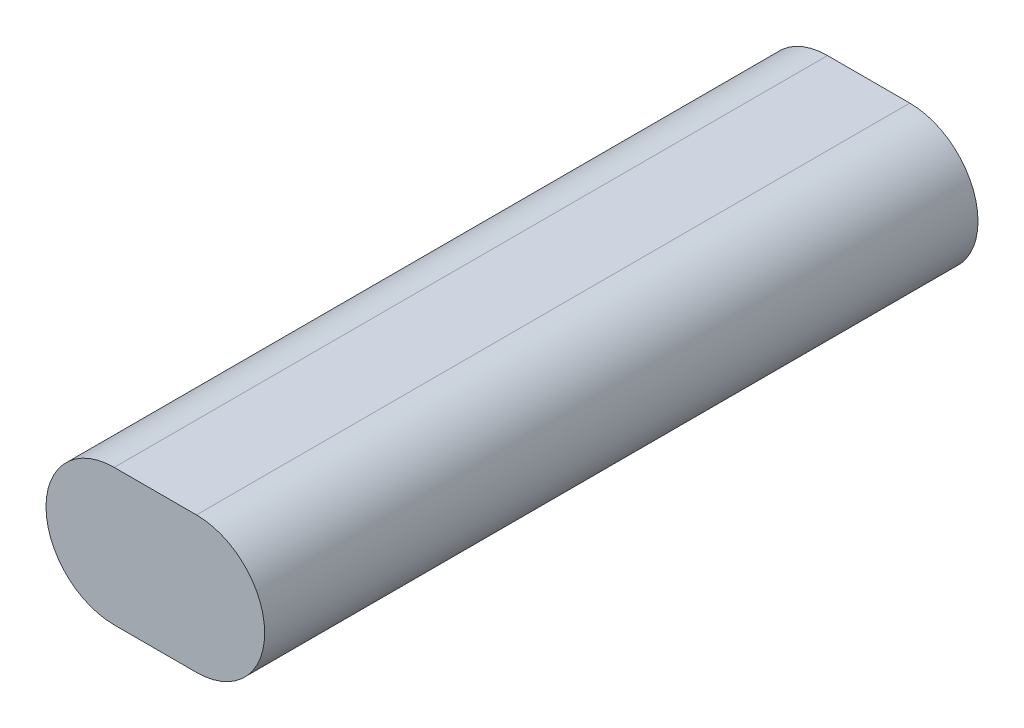
SolidWorks part; units mm, degrees
ref_plane "Front Plane" through (0, 0, 0) normal (0, 0, 1) x (1, 0, 0)
ref_plane "Top Plane" through (0, 0, 0) normal (0, 1, 0) x (1, 0, 0)
ref_plane "Right Plane" through (0, 0, 0) normal (1, 0, 0) x (0, 0, -1)
sketch "Sketch1" plane through (0, 0, 0) normal (0, 0, 1) x (1, 0, 0)
  line L0 (-12.573, 0) -> (12.573, 0) construction
  line L1 (-12.573, 11.557) -> (12.573, 11.557)
  line L2 (-12.573, -11.557) -> (12.573, -11.557)
  line L3 (-10.033, 0) -> (10.033, 0) construction
  line L4 (-10.033, 16.637) -> (10.033, 16.637)
  line L5 (-10.033, -16.637) -> (10.033, -16.637)
  line L6 (-24.13, 0) -> (-26.67, 0)
  line L7 (24.13, 0) -> (26.67, 0)
  arc A0 (-12.573, 11.557) -> (-12.573, -11.557) centre (-12.573, 0) ccw
  arc A1 (12.573, -11.557) -> (12.573, 11.557) centre (12.573, 0) ccw
  arc A2 (-10.033, 16.637) -> (-10.033, -16.637) centre (-10.033, 0) ccw
  arc A3 (10.033, -16.637) -> (10.033, 16.637) centre (10.033, 0) ccw
  point P2 (0, 0)
  point P8 (-24.13, 0)
  point P9 (24.13, 0)
  point P12 (0, 0)
  point P17 (-26.67, 0)
  dimension "D2" = 23.114
  dimension "D4" = 2.54
  dimension "D1" = 48.26
  dimension "D3" = 5.08
extrude "Boss-Extrude1" add sketch "Sketch1" against normal blind 168.91 contours L7 A3 L4 A2 L6 A0 L1 A1 | L5 A3 L7 A1 L2 A0 L6 A2
sketch "Sketch3" plane through (0, 0, 0) normal (0, 0, 1) x (1, 0, 0)
  line L0 (-10.033, 0) -> (10.033, 0) construction
  line L1 (-10.033, 16.637) -> (10.033, 16.637)
  line L2 (-10.033, -16.637) -> (10.033, -16.637)
  line L3 (-10.033, 16.637) -> (10.033, 16.637) construction
  arc A0 (-10.033, 16.637) -> (-10.033, -16.637) centre (-10.033, 0) ccw
  arc A1 (10.033, -16.637) -> (10.033, 16.637) centre (10.033, 0) ccw
  arc A2 (-10.033, 16.637) -> (-10.033, -16.637) centre (-10.033, 0) ccw construction
  point P2 (0, 0)
  point P8 (-26.67, 0)
  point P9 (-26.67, 0)
  dimension "D1" = 0
extrude "Boss-Extrude2" add sketch "Sketch3" along normal blind 5.08
sketch "Sketch4" plane through (0, 0, 0) normal (0, 0, 1) x (1, 0, 0)
  line L1 (-30.7622, 14.8905) -> (26.67, 14.8905)
  line L2 (-30.7622, 14.8905) -> (-30.7622, 0)
  line L3 (-30.7622, 0) -> (26.67, 0)
  line L4 (26.67, 14.8905) -> (26.67, 0)
  arc A0 (10.033, -16.637) -> (10.033, 16.637) centre (10.033, 0) ccw construction
sketch "Sketch5" plane through (0, -11.557, 0) normal (0, 1, 0) x (1, 0, 0)
  line L2 (-10.033, -5.08) -> (10.033, -5.08) construction
  line L3 (-10.033, 168.91) -> (10.033, 168.91) construction
  circle A0 centre (0, 110.998) radius 3.683
  circle A1 centre (0, 52.832) radius 3.683
  dimension "D1" = 7.366
  dimension "D3" = 7.366
  dimension "D2" = 57.912
  dimension "D4" = 57.912
extrude "Cut-Extrude2" cut sketch "Sketch5" against normal blind 4.191
sketch "Sketch6" plane through (0, -11.557, 0) normal (0, 1, 0) x (1, 0, 0)
  line L0 (-10.033, -5.08) -> (10.033, -5.08) construction
  line L1 (-10.033, 168.91) -> (10.033, 168.91) construction
  circle A0 centre (0, 110.998) radius 2.286
  circle A1 centre (0, 52.832) radius 2.286
  point P6 (0, 168.91)
  dimension "D3" = 4.572
  dimension "D4" = 4.572
  dimension "D1" = 57.912
  dimension "D2" = 57.912
extrude "Cut-Extrude3" cut sketch "Sketch6" against normal blind 6.731
